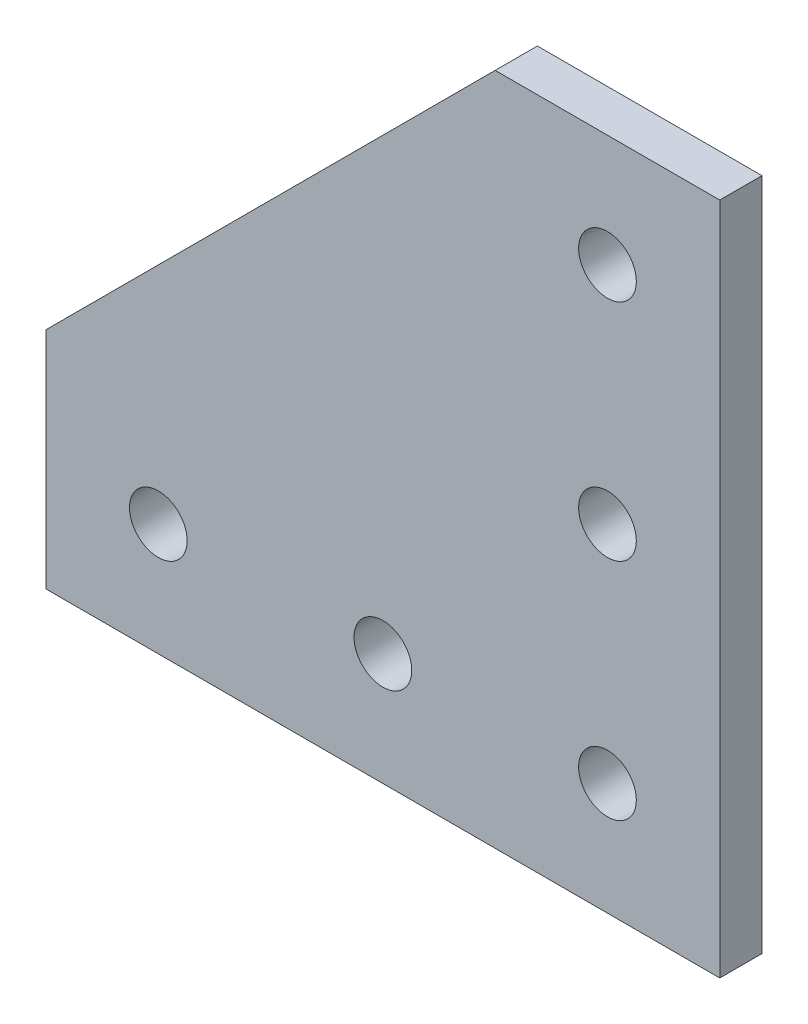
SolidWorks part; units mm, degrees
ref_plane "Front Plane" through (0, 0, 0) normal (0, 0, 1) x (1, 0, 0)
ref_plane "Top Plane" through (0, 0, 0) normal (0, 1, 0) x (1, 0, 0)
ref_plane "Right Plane" through (0, 0, 0) normal (1, 0, 0) x (0, 0, -1)
ref_plane "Plane1" through (0, 0, 0) normal (0, 0, 1) x (1, 0, 0)
sketch "Sketch1" plane through (0, 0, 0) normal (0, 0, 1) x (1, 0, 0)
  line L0 (-38.1, 0) -> (38.1, 0)
  line L1 (38.1, 0) -> (38.1, 76.2)
  line L2 (38.1, 76.2) -> (12.7, 76.2)
  line L3 (12.7, 76.2) -> (-38.1, 25.4)
  line L4 (-38.1, 25.4) -> (-38.1, 0)
  circle A0 centre (25.4, 63.5) radius 3.2639
  circle A1 centre (25.4, 38.1) radius 3.2639
  circle A2 centre (25.4, 12.7) radius 3.2639
  circle A3 centre (0, 12.7) radius 3.2639
  circle A4 centre (-25.4, 12.7) radius 3.2639
extrude "Boss-Extrude1" add sketch "Sketch1" along normal blind 4.7752
